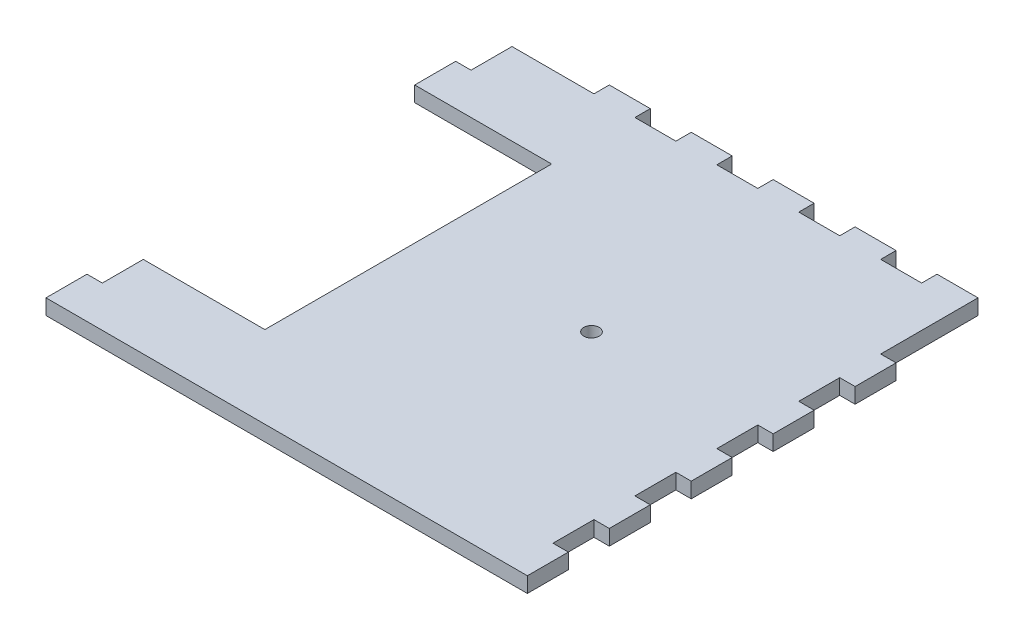
SolidWorks part; units mm, degrees
ref_plane "Front Plane" through (0, 0, 0) normal (0, 0, 1) x (1, 0, 0)
ref_plane "Top Plane" through (0, 0, 0) normal (0, 1, 0) x (1, 0, 0)
ref_plane "Right Plane" through (0, 0, 0) normal (1, 0, 0) x (0, 0, -1)
sketch "Sketch1" plane through (0, 0, 0) normal (0, 1, 0) x (1, 0, 0)
  line L1 (-139.7, -139.7) -> (139.7, -139.7)
  line L2 (-139.7, -139.7) -> (-139.7, 139.7)
  line L3 (-139.7, 139.7) -> (139.7, 139.7)
  line L4 (139.7, -139.7) -> (139.7, 139.7)
  line L5 (-139.7, -139.7) -> (139.7, 139.7) construction
  line L6 (-139.7, 139.7) -> (139.7, -139.7) construction
  point P0 (0, 0)
  dimension "D1" = 279.4
  dimension "D2" = 279.4
extrude "Boss-Extrude1" add sketch "Sketch1" along normal blind 9.525
sketch "Sketch2" plane through (139.7, 0, 0) normal (1, 0, 0) x (0, 0, -1)
  line L0 (-139.7, 9.525) -> (139.7, 9.525) construction
  line L1 (-139.7, 0) -> (-114.3, 0)
  line L2 (-139.7, 0) -> (-139.7, 9.525)
  line L3 (-139.7, 9.525) -> (-114.3, 9.525)
  line L4 (-114.3, 0) -> (-114.3, 9.525)
  dimension "D1" = 25.4
extrude "Boss-Extrude2" add sketch "Sketch2" along normal blind 9.525
pattern_linear "LPattern1" count 5 spacing 50.8 along (0, 0, -1) of "Boss-Extrude2"
mirror "Mirror1" about plane through (0, 0, 0) normal (1, 0, 0) of "LPattern1", "Boss-Extrude2"
sketch "Sketch3" plane through (0, 0, -139.7) normal (0, 0, -1) x (-1, 0, 0)
  line L0 (-139.7, 9.525) -> (139.7, 9.525) construction
  line L1 (-139.7, 9.525) -> (-114.3, 9.525)
  line L2 (-139.7, 9.525) -> (-139.7, 0)
  line L3 (-139.7, 0) -> (-114.3, 0)
  line L4 (-114.3, 9.525) -> (-114.3, 0)
  line L5 (-139.7, 0) -> (139.7, 0) construction
  line L7 (-149.225, 0) -> (-149.225, 9.525) construction
  dimension "D1" = 9.525
  dimension "D2" = 25.4
extrude "Boss-Extrude3" add sketch "Sketch3" along normal blind 9.525
pattern_linear "LPattern2" count 5 spacing 50.8 along (-1, 0, 0) of "Boss-Extrude3"
sketch "Sketch6" plane through (0, 9.525, 0) normal (0, 1, 0) x (1, 0, 0)
  line L0 (63.5, 139.7) -> (38.1, 139.7) construction
  line L1 (139.7, -12.7) -> (139.7, 12.7) construction
  circle A0 centre (38.1, 11.176) radius 4.7625
  dimension "D1" = 128.524
  dimension "D3" = 9.525
  dimension "D2" = 101.6
extrude "Cut-Extrude1" cut sketch "Sketch6" against normal through all
sketch "Sketch8" plane through (0, 9.525, 0) normal (0, 1, 0) x (1, 0, 0)
  line L1 (-149.225, 88.9) -> (-64.3339, 88.9)
  line L2 (-149.225, 88.9) -> (-149.225, -88.9)
  line L3 (-149.225, -88.9) -> (-64.3339, -88.9)
  line L4 (-64.3339, 88.9) -> (-64.3339, -88.9)
  dimension "D1" = 177.8
extrude "Cut-Extrude3" cut sketch "Sketch8" against normal through all
sketch "Sketch7" plane through (0, 9.525, 0) normal (0, 1, 0) x (1, 0, 0)
  line L2 (-88.9, 139.7) -> (-139.7, 139.7) construction
  line L3 (-139.7, 139.7) -> (-139.7, 88.9) construction
  circle A0 centre (-101.6, 65.278) radius 5.08
  circle A1 centre (-101.6, 27.686) radius 5.08
  dimension "D1" = 10.16
  dimension "D2" = 10.16
  dimension "D3" = 38.1
  dimension "D5" = 37.592
  dimension "D6" = 74.422
sketch "Sketch9" plane through (-139.7, 0, 0) normal (-1, 0, 0) x (0, 0, 1)
  line L0 (158.9088, 0) -> (-158.9088, 0) construction
  line L1 (-88.9, 9.525) -> (-114.3, 9.525)
  line L2 (-88.9, 9.525) -> (-88.9, 0)
  line L3 (-88.9, 0) -> (-114.3, 0)
  line L4 (-114.3, 9.525) -> (-114.3, 0)
  dimension "D1" = 25.4
extrude "Boss-Extrude4" add sketch "Sketch9" along normal blind 9.525
